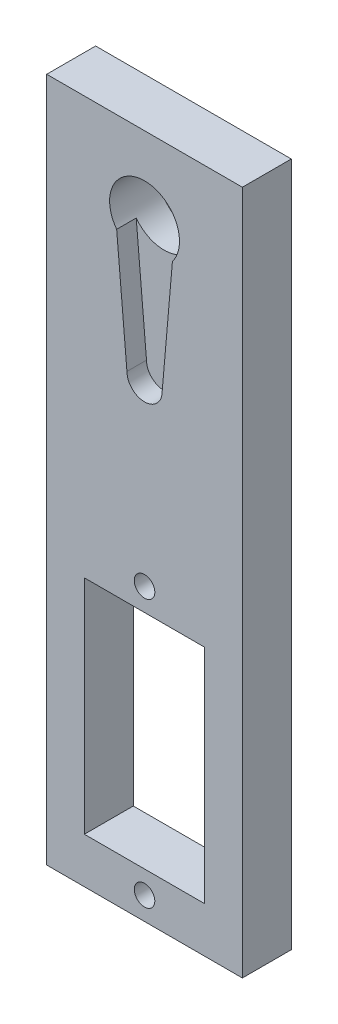
SolidWorks part; units mm, degrees
ref_plane "Front Plane" through (0, 0, 0) normal (0, 0, 1) x (1, 0, 0)
ref_plane "Top Plane" through (0, 0, 0) normal (0, 1, 0) x (1, 0, 0)
ref_plane "Right Plane" through (0, 0, 0) normal (1, 0, 0) x (0, 0, -1)
sketch "Sketch3" plane through (0, 0, 0) normal (0, 0, 1) x (1, 0, 0)
  line L1 (-10, 35) -> (10, 35)
  line L2 (-10, 35) -> (-10, -35)
  line L3 (-10, -35) -> (10, -35)
  line L4 (10, 35) -> (10, -35)
  line L5 (-10, 35) -> (10, -35) construction
  line L6 (-10, -35) -> (10, 35) construction
  point P0 (0, 0)
  dimension "D1" = 20
  dimension "D2" = 70
extrude "Boss-Extrude3" add sketch "Sketch3" along normal blind 5
sketch "Sketch4" plane through (0, 0, 5) normal (0, 0, 1) x (1, 0, 0)
  line L0 (-1.8, 12.7957) -> (1.8, 12.7957)
  line L1 (-2.85, 24.85) -> (2.85, 24.85)
  line L2 (-2.85, 24.85) -> (-1.8, 12.7957)
  line L3 (2.85, 24.85) -> (1.8, 12.7957)
  line L4 (10, -35) -> (10, 35) construction
  line L7 (10, 35) -> (-10, 35) construction
  circle A0 centre (0, 27) radius 3.57
  arc A1 (-1.8, 12.7957) -> (1.8, 12.7957) centre (0, 12.7957) ccw
  dimension "D1" = 7.14
  dimension "D2" = 3.6
  dimension "D3" = 5.7
  dimension "D4" = 12.1
  dimension "D5" = 12.1
  dimension "D6" = 10
  dimension "D7" = 8
extrude "Cut-Extrude2" cut sketch "Sketch4" against normal blind 2 contours L0 A1 | A0 L2 L0 L3
sketch "Sketch6" plane through (0, 0, 3) normal (0, 0, 1) x (1, 0, 0)
  line L0 (10, 35) -> (-10, 35) construction
  line L1 (-10, 35) -> (-10, -35) construction
  circle A0 centre (0, 27) radius 3.57
  dimension "D1" = 7.14
  dimension "D2" = 8
  dimension "D3" = 10
extrude "Cut-Extrude3" cut sketch "Sketch6" against normal blind 3
sketch "Sketch7" plane through (0, 0, 5) normal (0, 0, 1) x (1, 0, 0)
  line L0 (10, -35) -> (10, 35) construction
  line L1 (-6.15, -7.65) -> (6.15, -7.65)
  line L2 (-6.15, -7.65) -> (-6.15, -30.35)
  line L3 (-6.15, -30.35) -> (6.15, -30.35)
  line L4 (6.15, -7.65) -> (6.15, -30.35)
  line L5 (-6.15, -7.65) -> (6.15, -30.35) construction
  line L6 (-6.15, -30.35) -> (6.15, -7.65) construction
  line L7 (-10, -35) -> (10, -35) construction
  line L8 (0, -19) -> (16.5777, -19) construction
  circle A0 centre (0, -5.33) radius 1.05
  circle A1 centre (0, -32.67) radius 1.05
  point P0 (0, -19)
  dimension "D6" = 2.1
  dimension "D1" = 12.3
  dimension "D2" = 22.7
  dimension "D3" = 10
  dimension "D4" = 16
  dimension "D5" = 10
  dimension "D7" = 2.32
extrude "Cut-Extrude4" cut sketch "Sketch7" against normal blind 5
